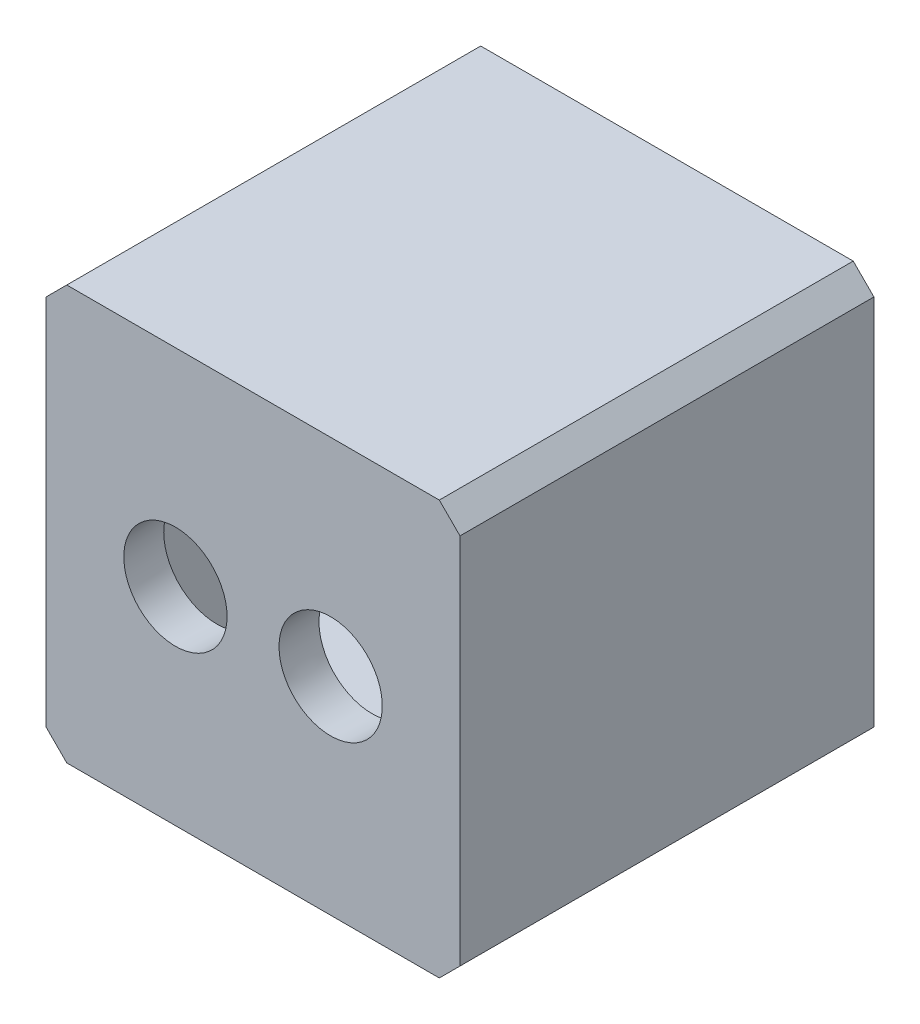
SolidWorks part; units mm, degrees
ref_plane "Plan de face" through (0, 0, 0) normal (0, 0, 1) x (1, 0, 0)
ref_plane "Plan de dessus" through (0, 0, 0) normal (0, 1, 0) x (1, 0, 0)
ref_plane "Plan de droite" through (0, 0, 0) normal (1, 0, 0) x (0, 0, -1)
sketch "Esquisse1" plane through (0, 0, 0) normal (0, 0, 1) x (1, 0, 0)
  line L1 (-34.6304, 29.1827) -> (-14.6304, 29.1827)
  line L2 (-34.6304, 29.1827) -> (-34.6304, 9.1827)
  line L3 (-34.6304, 9.1827) -> (-14.6304, 9.1827)
  line L4 (-14.6304, 29.1827) -> (-14.6304, 9.1827)
  dimension "D1" = 20
  dimension "21" = 20
extrude "Boss.-Extru.1" add sketch "Esquisse1" along normal blind 20
sketch "Esquisse2" plane through (0, 0, 20) normal (0, 0, 1) x (1, 0, 0)
  line L0 (-24.6304, 29.1827) -> (-24.6304, 9.1827) construction
  line L1 (-14.6304, 29.1827) -> (-34.6304, 29.1827) construction
  line L2 (-34.6304, 9.1827) -> (-14.6304, 9.1827) construction
  line L3 (-34.6304, 19.1827) -> (-14.6304, 19.1827) construction
  line L4 (-34.6304, 29.1827) -> (-34.6304, 9.1827) construction
  line L5 (-14.6304, 9.1827) -> (-14.6304, 29.1827) construction
  circle A0 centre (-28.3804, 19.1827) radius 2.6
  circle A1 centre (-20.8804, 19.1827) radius 2.6
  dimension "D1" = 5.2
  dimension "D2" = 7.5
extrude "Enlèv. mat.-Extru.1" cut sketch "Esquisse2" along normal through all draft 2 from offset 3 offset against normal yes
sketch "Esquisse3" plane through (0, 0, 0) normal (0, 0, -1) x (-1, 0, 0)
  line L0 (14.6304, 9.1827) -> (14.6304, 29.1827) construction
  line L1 (16.6304, 27.1827) -> (32.6304, 27.1827)
  line L2 (16.6304, 27.1827) -> (16.6304, 11.1827)
  line L3 (16.6304, 11.1827) -> (32.6304, 11.1827)
  line L4 (32.6304, 27.1827) -> (32.6304, 11.1827)
  line L5 (14.6304, 29.1827) -> (34.6304, 29.1827) construction
  line L6 (14.6304, 19.1827) -> (34.6304, 19.1827) construction
  line L7 (34.6304, 29.1827) -> (34.6304, 9.1827) construction
  line L8 (24.6304, 29.1827) -> (24.6304, 9.1827) construction
  line L9 (34.6304, 9.1827) -> (14.6304, 9.1827) construction
  dimension "D1" = 2
  dimension "2" = 2
extrude "Enlèv. mat.-Extru.2" cut sketch "Esquisse3" against normal blind 18
chamfer "Chanfrein1" distance 1 angle 45 4 edges at (-14.6304, 9.1827, 10) (-14.6304, 29.1827, 10) (-34.6304, 29.1827, 10) (-34.6304, 9.1827, 10)
